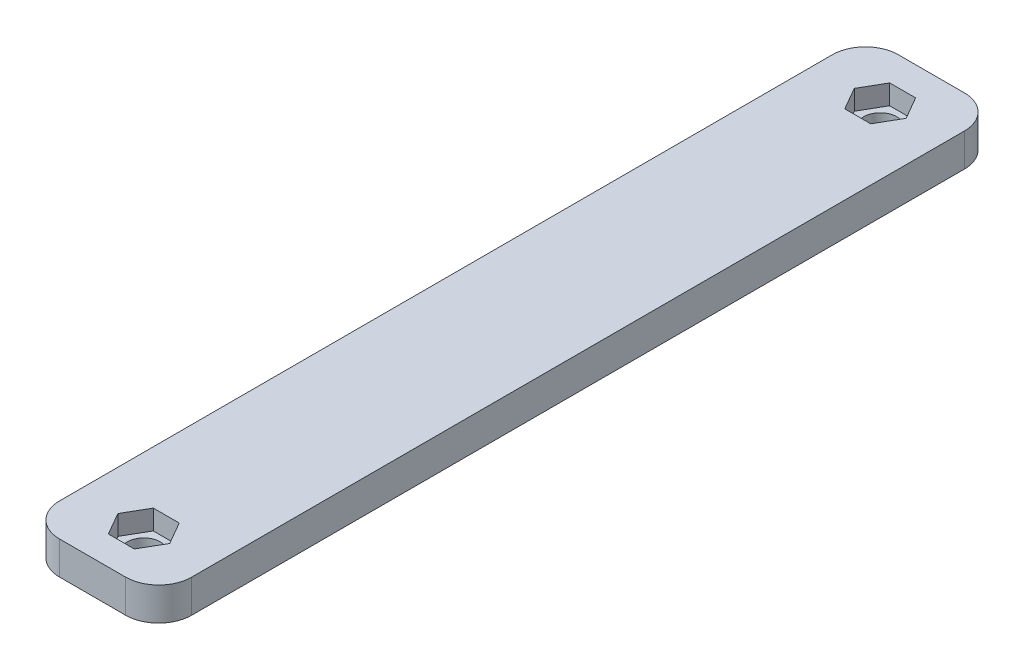
SolidWorks part; units mm, degrees
ref_plane "Front Plane" through (0, 0, 0) normal (0, 0, 1) x (1, 0, 0)
ref_plane "Top Plane" through (0, 0, 0) normal (0, 1, 0) x (1, 0, 0)
ref_plane "Right Plane" through (0, 0, 0) normal (1, 0, 0) x (0, 0, -1)
sketch "Sketch1" plane through (0, 0, 0) normal (0, 1, 0) x (1, 0, 0)
  line L1 (-10, -63.5) -> (10, -63.5)
  line L2 (-10, -63.5) -> (-10, 63.5)
  line L3 (-10, 63.5) -> (10, 63.5)
  line L4 (10, -63.5) -> (10, 63.5)
  line L5 (-10, -63.5) -> (10, 63.5) construction
  line L6 (-10, 63.5) -> (10, -63.5) construction
  point P0 (0, 0)
  dimension "D1" = 20
  dimension "D2" = 127
extrude "Boss-Extrude1" add sketch "Sketch1" along normal blind 5
sketch "Sketch3" plane through (0, 5, 0) normal (0, 1, 0) x (1, 0, 0)
  line L0 (10, 63.5) -> (-10, 63.5) construction
  line L1 (3.926, 55.75) -> (1.963, 59.15)
  line L2 (1.963, 59.15) -> (-1.963, 59.15)
  line L3 (-1.963, 59.15) -> (-3.926, 55.75)
  line L4 (-3.926, 55.75) -> (-1.963, 52.35)
  line L5 (-1.963, 52.35) -> (1.963, 52.35)
  line L6 (1.963, 52.35) -> (3.926, 55.75)
  circle A0 centre (0, 55.75) radius 3.4 construction
  point P1 (0, 0)
  point P10 (0, 16.8307)
  dimension "D1" = 6.8
  dimension "D2" = 7.75
extrude "Cut-Extrude1" cut sketch "Sketch3" against normal blind 3
sketch "Sketch4" plane through (0, 2, 0) normal (0, 1, 0) x (1, 0, 0)
  line L0 (-3.926, 55.75) -> (3.926, 55.75) construction
  line L1 (0, 59.15) -> (0, 52.35) construction
  line L2 (1.963, 59.15) -> (-1.963, 59.15) construction
  line L3 (-1.963, 52.35) -> (1.963, 52.35) construction
  circle A0 centre (0, 55.75) radius 2.5
  point P13 (0, 15.4)
  dimension "D1" = 5
extrude "Cut-Extrude2" cut sketch "Sketch4" against normal through all
mirror "Mirror1" about plane through (0, 0, 0) normal (0, 0, 1) of "Cut-Extrude1", "Cut-Extrude2"
fillet "Fillet1" radius 5 4 edges at (-10, 2.5, -63.5) (10, 2.5, -63.5) (10, 2.5, 63.5) (-10, 2.5, 63.5)
